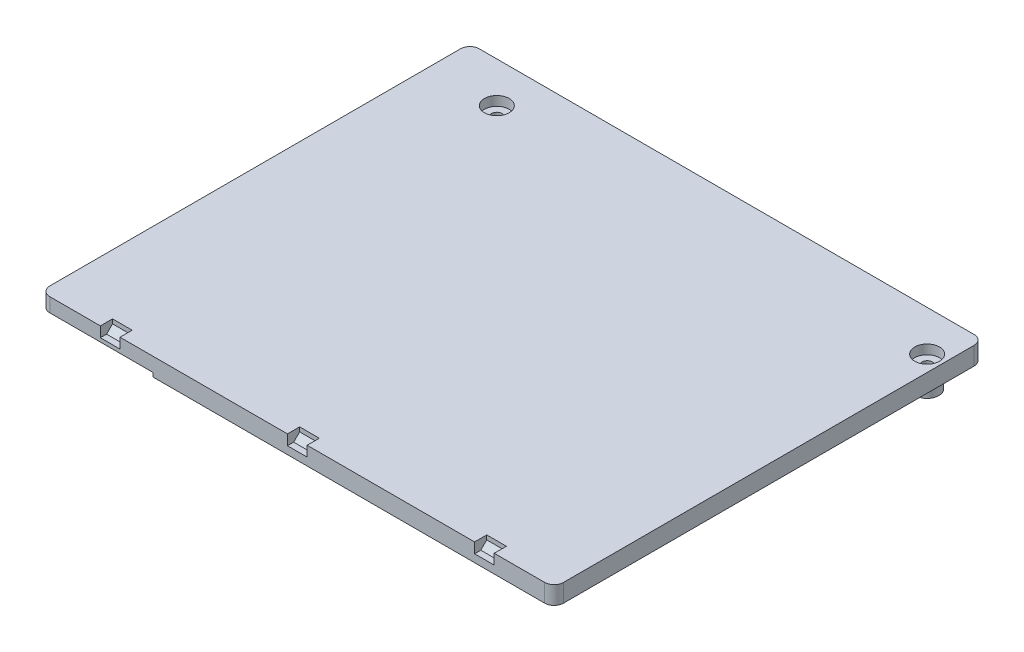
SolidWorks part; units mm, degrees
ref_plane "前视基准面" through (0, 0, 0) normal (0, 0, 1) x (1, 0, 0)
ref_plane "上视基准面" through (0, 0, 0) normal (0, 1, 0) x (1, 0, 0)
ref_plane "右视基准面" through (0, 0, 0) normal (1, 0, 0) x (0, 0, -1)
sketch "草图1" plane through (0, 0, 0) normal (0, 1, 0) x (1, 0, 0)
  line L1 (-52.9, -45.9) -> (52.9, -45.9)
  line L2 (-54.9, -43.9) -> (-54.9, 43.9)
  line L3 (-52.9, 45.9) -> (52.9, 45.9)
  line L4 (54.9, -43.9) -> (54.9, 43.9)
  line L5 (-54.9, -45.9) -> (54.9, 45.9) construction
  line L6 (-54.9, 45.9) -> (54.9, -45.9) construction
  arc A0 (-52.9, -45.9) -> (-54.9, -43.9) centre (-52.9, -43.9) cw
  arc A1 (52.9, -45.9) -> (54.9, -43.9) centre (52.9, -43.9) ccw
  arc A2 (52.9, 45.9) -> (54.9, 43.9) centre (52.9, 43.9) cw
  arc A3 (-54.9, 43.9) -> (-52.9, 45.9) centre (-52.9, 43.9) cw
  point P0 (0, 0)
  dimension "D3" = 2
  dimension "D1" = 91.8
  dimension "D2" = 109.8
extrude "凸台-拉伸1" add sketch "草图1" along normal blind 3.85
sketch "草图2" plane through (0, 3.85, 0) normal (0, 1, 0) x (1, 0, 0)
  line L0 (-40.5, 37.25) -> (51.5, 37.25) construction
  line L1 (52.9, 45.9) -> (-52.9, 45.9) construction
  line L2 (54.9, -43.9) -> (54.9, 43.9) construction
  circle A0 centre (-40.5, 37.25) radius 1.1
  circle A1 centre (51.5, 37.25) radius 1.1
  dimension "D1" = 2.2
  dimension "D2" = 92
  dimension "D3" = 8.65
  dimension "D4" = 3.4
extrude "切除-拉伸1" cut sketch "草图2" against normal through all
sketch "草图3" plane through (0, 0, 0) normal (1, 0, 0) x (0, 0, -1)
  line L0 (-45.9, 3.85) -> (-43.3, 3.85)
  line L1 (-43.9, 3.85) -> (43.9, 3.85) construction
  line L3 (-45.9, 3.85) -> (-45.9, 0) construction
  line L4 (-45.9, 1.65) -> (-45.9, 3.85)
  line L5 (-45.9, 1.65) -> (-44.5728, 1.65)
  line L7 (-43.3, 3.85) -> (-43.3, 2.9228)
  line L8 (-43.3, 2.9228) -> (-44.5728, 1.65)
  point P5 (-42.9198, 3.5)
  point P10 (-43.2978, 3.0813)
  dimension "D1" = 1.8
  dimension "D2" = 135
  dimension "D3" = 2.2
  dimension "D4" = 2.6
extrude "切除-拉伸2" cut sketch "草图3" against normal mid plane 4.2
pattern_linear "阵列(线性)1" count 2 spacing 40 along (1, 0, 0) of "切除-拉伸2"
pattern_linear "阵列(线性)2" count 2 spacing 40 along (-1, 0, 0) of "切除-拉伸2"
sketch "草图7" plane through (0, 0, 0) normal (0, -1, 0) x (1, 0, 0)
  line L0 (-28.5, 38.9) -> (-1.5, 38.9) construction
  line L1 (-28.5, 40.9) -> (-1.5, 40.9)
  line L2 (-28.5, 36.9) -> (-1.5, 36.9)
  line L3 (-40.5, -37.25) -> (-40.5, 43.1647) construction
  line L4 (-52.9, 45.9) -> (52.9, 45.9) construction
  line L5 (45.5, 28.75) -> (45.5, 6.75) construction
  line L6 (47.5, 28.75) -> (47.5, 6.75)
  line L7 (43.5, 28.75) -> (43.5, 6.75)
  line L8 (-7.5, -37.75) -> (42.5, -37.75) construction
  line L9 (-7.5, -35.75) -> (42.5, -35.75)
  line L10 (-7.5, -39.75) -> (42.5, -39.75)
  line L11 (51.5, -37.25) -> (23.8548, -37.25) construction
  circle A0 centre (-40.5, -37.25) radius 2.5
  circle A1 centre (51.5, -37.25) radius 2.5
  circle A3 centre (51.5, -37.25) radius 1.1 construction
  circle A4 centre (51.5, -37.25) radius 1.1
  circle A5 centre (-40.5, -37.25) radius 1.1 construction
  circle A6 centre (-40.5, -37.25) radius 1.1
  arc A8 (-28.5, 40.9) -> (-28.5, 36.9) centre (-28.5, 38.9) ccw
  arc A9 (-1.5, 36.9) -> (-1.5, 40.9) centre (-1.5, 38.9) ccw
  circle A10 centre (-11.5, 19.75) radius 2.5
  arc A13 (47.5, 28.75) -> (43.5, 28.75) centre (45.5, 28.75) ccw
  arc A14 (43.5, 6.75) -> (47.5, 6.75) centre (45.5, 6.75) ccw
  arc A15 (-7.5, -35.75) -> (-7.5, -39.75) centre (-7.5, -37.75) ccw
  arc A16 (42.5, -39.75) -> (42.5, -35.75) centre (42.5, -37.75) ccw
  circle A17 centre (-22.5, -14.25) radius 2.5
  circle A18 centre (12.5, 8.75) radius 2.5
  point P14 (-15, 38.9)
  point P28 (45.5, 17.75)
  point P33 (17.5, -37.75)
  dimension "D1" = 5
  dimension "D2" = 2
  dimension "D3" = 10
  dimension "D5" = 41
  dimension "D8" = 5
  dimension "D10" = 42
  dimension "D11" = 68
  dimension "D13" = 31
  dimension "D14" = 85
  dimension "D4" = 5
  dimension "D6" = 29
  dimension "D7" = 57
  dimension "D9" = 84
  dimension "D12" = 1.5
  dimension "D15" = 18
  dimension "D16" = 53
  dimension "D17" = 46
  dimension "D18" = 23
extrude "凸台-拉伸2" add sketch "草图7" along normal blind 2.6
sketch "草图8" plane through (0, 3.85, 0) normal (0, 1, 0) x (1, 0, 0)
  circle A0 centre (-40.5, 37.25) radius 2.65
  circle A1 centre (51.5, 37.25) radius 2.65
  dimension "D1" = 5.3
extrude "切除-拉伸5" cut sketch "草图8" against normal blind 2
sketch "草图5" plane through (0, 0, 0) normal (0, -1, 0) x (1, 0, 0)
  line L1 (36.5, 43.75) -> (19.5, 43.75)
  line L2 (36.5, 43.75) -> (36.5, 20.75)
  line L3 (36.5, 20.75) -> (19.5, 20.75)
  line L4 (19.5, 43.75) -> (19.5, 20.75)
  point P5 (51.5, -37.25)
  dimension "D3" = 81
  dimension "D4" = 32
  dimension "D1" = 58
  dimension "D2" = 15
extrude "切除-拉伸3" cut sketch "草图5" against normal offset from surface (1.85 mm away) 2 up to face at (-40.5, 3.85, -34.6)
sketch "草图6" plane through (0, 0, 0) normal (0, -1, 0) x (1, 0, 0)
  circle A0 centre (46.5, 0.75) radius 4
  point P2 (51.5, -37.25)
  point P3 (45.1433, 0.75)
  dimension "D1" = 8
  dimension "D2" = 38
  dimension "D3" = 5
extrude "切除-拉伸4" cut sketch "草图6" against normal offset from surface (1.85 mm away) 2 up to face at (-40.5, 3.85, -34.6)
sketch "草图9" plane through (0, 0, 0) normal (0, -1, 0) x (1, 0, 0)
  line L0 (-52.9, 45.9) -> (52.9, 45.9) construction
  line L1 (-30.9, 45.9) -> (-54.9, 45.9)
  line L2 (-30.9, 45.9) -> (-30.9, -21.1)
  line L3 (-30.9, -21.1) -> (-54.9, -21.1)
  line L4 (-54.9, 45.9) -> (-54.9, -21.1)
  line L5 (-54.9, -43.9) -> (-54.9, 43.9) construction
  dimension "D1" = 67
  dimension "D2" = 24
extrude "切除-拉伸6" cut sketch "草图9" against normal offset from surface (0.85 mm away) 3 up to face at (-40.5, 3.85, -34.6)
sketch "草图10" plane through (0, 0, 0) normal (0, -1, 0) x (1, 0, 0)
  line L0 (-37.4, 11.75) -> (-37.4, -16.75) construction
  circle A0 centre (-37.4, 11.75) radius 3
  circle A1 centre (-37.4, -16.75) radius 3
  point P4 (-40.5, -37.25)
  point P5 (-37.6099, -4.997)
  dimension "D2" = 6
  dimension "D1" = 28.5
  dimension "D3" = 20.5
  dimension "D4" = 3.1
extrude "切除-拉伸7" cut sketch "草图10" against normal offset from surface (2.65 mm away) 1.2 up to face at (-40.5, 3.85, -34.6)
sketch "草图11" plane through (0, 0, 0) normal (0, -1, 0) x (1, 0, 0)
  circle A0 centre (-26.5, 6.75) radius 4.5
  point P2 (-40.5, -37.25)
  dimension "D1" = 9
  dimension "D2" = 14
  dimension "D3" = 44
extrude "切除-拉伸8" cut sketch "草图11" against normal offset from surface (2.85 mm away) 1 up to face at (-40.5, 3.85, -34.6)
